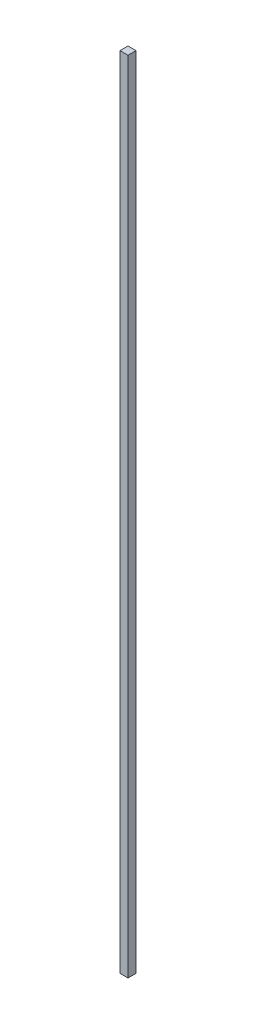
SolidWorks part; units mm, degrees
ref_plane "Front Plane" through (0, 0, 0) normal (0, 0, 1) x (1, 0, 0)
ref_plane "Top Plane" through (0, 0, 0) normal (0, 1, 0) x (1, 0, 0)
ref_plane "Right Plane" through (0, 0, 0) normal (1, 0, 0) x (0, 0, -1)
sketch "Sketch1" plane through (0, 0, 0) normal (0, 1, 0) x (1, 0, 0)
  line L1 (0, 0) -> (20, 0)
  line L2 (0, 0) -> (0, -20)
  line L3 (0, -20) -> (20, -20)
  line L4 (20, 0) -> (20, -20)
extrude "Boss-Extrude1" add sketch "Sketch1" along normal blind 2000
